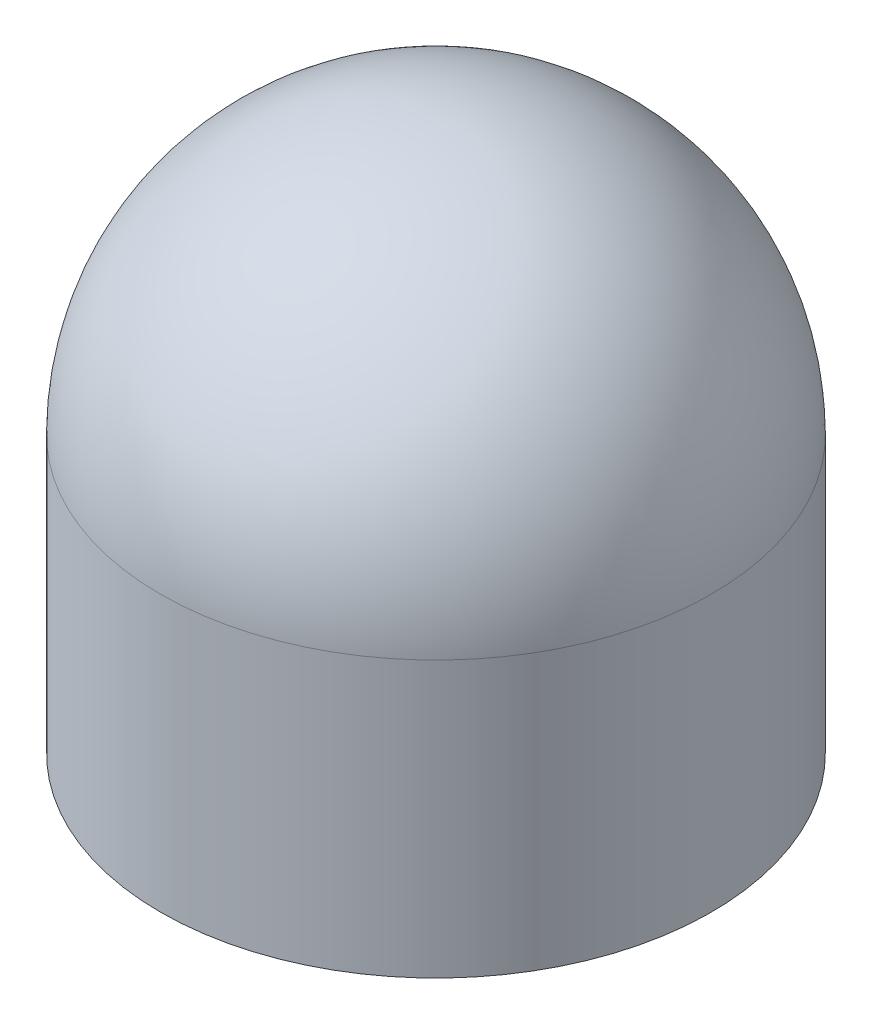
SolidWorks part; units mm, degrees
ref_plane "Front Plane" through (0, 0, 0) normal (0, 0, 1) x (1, 0, 0)
ref_plane "Top Plane" through (0, 0, 0) normal (0, 1, 0) x (1, 0, 0)
ref_plane "Right Plane" through (0, 0, 0) normal (1, 0, 0) x (0, 0, -1)
sketch "Sketch1" plane through (0, 0, 0) normal (0, 1, 0) x (1, 0, 0)
  circle A0 centre (-37.1905, 7.6987) radius 3
extrude "Boss-Extrude1" add sketch "Sketch1" along normal blind 3
sketch "Sketch2" plane through (0, 3, 0) normal (0, 1, 0) x (1, 0, 0)
  line L0 (-37.1905, 10.6987) -> (-37.1905, 4.6987)
  circle A0 centre (-37.1905, 7.6987) radius 3 construction
  arc A1 (-37.1905, 10.6987) -> (-37.1905, 4.6987) centre (-37.1905, 7.6987) ccw
revolve "Revolve1" add sketch "Sketch2" angle 360 about L0
